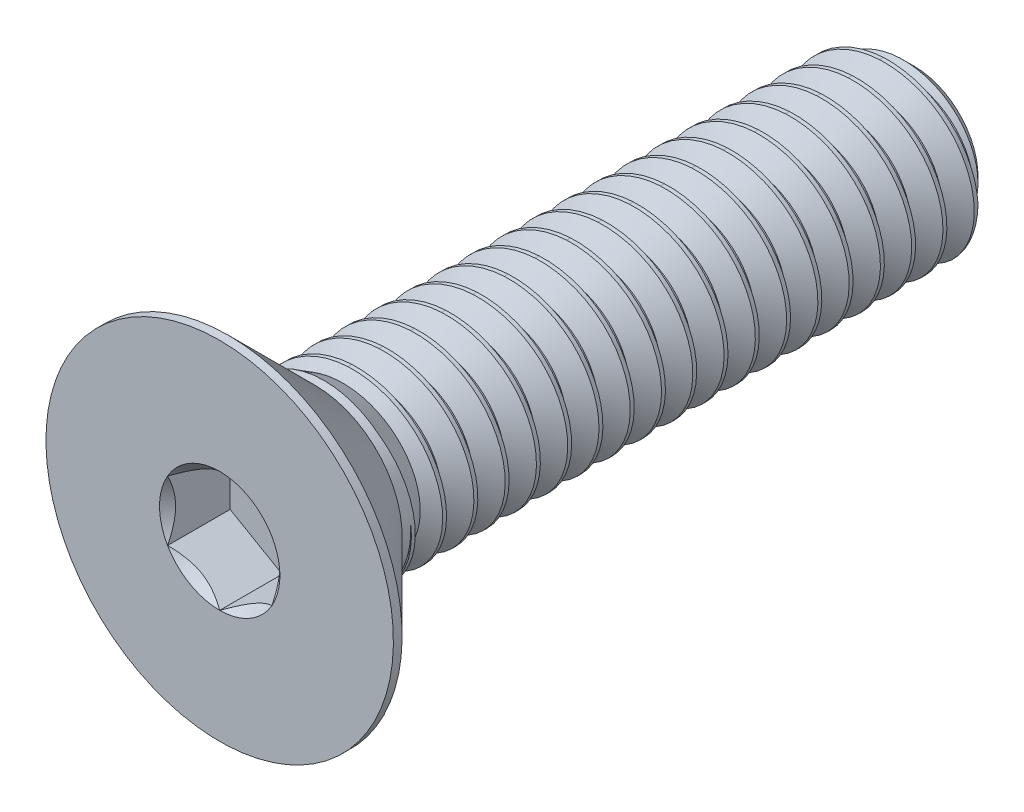
SolidWorks part; units mm, degrees
ref_plane "Front" through (0, 0, 0) normal (0, 0, 1) x (1, 0, 0)
ref_plane "Top" through (0, 0, 0) normal (0, 1, 0) x (1, 0, 0)
ref_plane "Right" through (0, 0, 0) normal (1, 0, 0) x (0, 0, -1)
sketch "Sketch1" plane through (0, 0, 0) normal (0, 0, 1) x (1, 0, 0)
  line L1 (0.75, 0.433) -> (0, 0.866)
  line L8 (0, 0.866) -> (-0.75, 0.433)
  line L9 (-0.75, 0.433) -> (-0.75, -0.433)
  line L10 (-0.75, -0.433) -> (0, -0.866)
  line L11 (0, -0.866) -> (0.75, -0.433)
  line L12 (0.75, -0.433) -> (0.75, 0.433)
  circle A0 centre (0, 0) radius 0.75 construction
  circle A1 centre (0, 0) radius 2.5
  point P7 (0, 2.5)
  dimension "Head Dia" = 5
  dimension "Hex" = 1.5
sketch "Sketch2" plane through (0, 0, 0) normal (1, 0, 0) x (0, 0, -1)
  line L2 (0, 0) -> (8.5, 0) construction
  line L3 (8.5, 0) -> (8.5, 1.25)
  line L6 (8.5, 1.25) -> (0, 1.25)
  line L8 (0, 1.25) -> (-0.125, 1.25)
  line L9 (-0.125, 1.25) -> (-1.375, 2.5)
  line L11 (-1.375, 2.5) -> (-1.5, 2.5)
  line L13 (-1.5, 2.5) -> (-1.5, 0)
  line L14 (-1.5, 0) -> (0, 0) construction
  line L15 (8.4719, 1.2987) -> (8.6969, 0.909) construction
  line L16 (8.6969, 0.909) -> (8.9219, 1.2987) construction
  line L17 (8.9219, 1.2987) -> (8.4719, 1.2987) construction
  line L18 (8.4859, 1.2744) -> (8.9078, 1.2744)
  line L19 (8.9078, 1.2744) -> (8.725, 0.9577)
  line L20 (8.725, 0.9577) -> (8.6688, 0.9577)
  line L21 (8.6688, 0.9577) -> (8.4859, 1.2744)
  line L22 (8.6969, 0.9577) -> (8.6969, 0.909) construction
  line L23 (8.5, 1.25) -> (8.8938, 1.25) construction
  line L24 (8.6969, 1.2987) -> (8.6969, 1.25) construction
  line L25 (8.5, 0.9125) -> (8.1625, 1.25)
  line L26 (8.5, -1.25) -> (0, -1.25)
  point P28 (8.6969, 1.2744)
  point P32 (7.825, -1.25)
  point P33 (-0.6, 0)
  point P35 (-1.5, 2.5)
  dimension "Dia" = 2.5
  dimension "Head Ht" = 1.5
  dimension "D2" = 45
  dimension "Lg" = 10
  dimension "Pitch" = 0.45
  dimension "D3" = 0.0563
  dimension "D1" = 45
  dimension "D4" = 0.3375
  dimension "D5" = 0.675
  dimension "D6" = 0.9
sketch "Sketch7" plane through (0, 0, 0) normal (1, 0, 0) x (0, 0, -1)
  line L2 (-1.5, 0) -> (-1.5, 2.5)
  line L3 (-1.5, 2.5) -> (-1.375, 2.5)
  line L5 (-1.375, 2.5) -> (-0.125, 1.25)
  line L6 (-0.125, 1.25) -> (8.1625, 1.25)
  line L8 (8.1625, 1.25) -> (8.5, 0.9125)
  line L9 (8.5, 0.9125) -> (8.5, 0)
  line L11 (8.5, 0) -> (-1.5, 0)
revolve "Revolve2" add sketch "Sketch7" angle 360 mid plane about L11
sketch "Sketch5" plane through (0, 0, 1.5) normal (0, 0, 1) x (1, 0, 0)
  line L0 (0.75, -0.433) -> (0.75, 0.433) construction
  line L1 (0, -0.866) -> (0.75, -0.433) construction
  line L2 (-0.75, -0.433) -> (0, -0.866) construction
  line L3 (-0.75, 0.433) -> (-0.75, -0.433) construction
  line L4 (0, 0.866) -> (-0.75, 0.433) construction
  line L5 (0.75, 0.433) -> (0, 0.866) construction
  line L6 (0.75, -0.433) -> (0.75, 0.433)
  line L7 (0, -0.866) -> (0.75, -0.433)
  line L8 (-0.75, -0.433) -> (0, -0.866)
  line L9 (-0.75, 0.433) -> (-0.75, -0.433)
  line L10 (0, 0.866) -> (-0.75, 0.433)
  line L11 (0.75, 0.433) -> (0, 0.866)
extrude "Cut-Extrude2" cut sketch "Sketch5" against normal up to vertex (0.9 mm away) up to point (0, 0, 0.6)
sketch "Sketch6" plane through (0, 0, 1.5) normal (0, 0, 1) x (1, 0, 0)
  circle A0 centre (0, 0) radius 0.866
extrude "Cut-Extrude3" cut sketch "Sketch6" against normal up to vertex (0.9 mm away) draft 45 up to point (0, 0, 0.6)
sketch "Sketch3" plane through (0, 0, -8.5) normal (0, 0, -1) x (-1, 0, 0)
  circle A0 centre (0, 0) radius 1.25
split "Split1" trim tools "Front" bodies to split 113 resulting bodies 125 126
curve "Helix/Spiral1" pitch 0.45 height 8.95 turns 19.8889
sketch "Sketch8" plane through (0, 0, 0) normal (1, 0, 0) x (0, 0, -1)
  line L0 (8.4859, 1.2744) -> (8.9078, 1.2744) construction
  line L1 (8.6688, 0.9577) -> (8.4859, 1.2744) construction
  line L2 (8.725, 0.9577) -> (8.6688, 0.9577) construction
  line L3 (8.9078, 1.2744) -> (8.725, 0.9577) construction
  line L4 (8.4859, 1.2744) -> (8.9078, 1.2744)
  line L5 (8.6688, 0.9577) -> (8.4859, 1.2744)
  line L6 (8.725, 0.9577) -> (8.6688, 0.9577)
  line L7 (8.9078, 1.2744) -> (8.725, 0.9577)
sweep "Cut-Sweep1" cut profiles "Sketch8" path "Helix/Spiral1"
sketch "Sketch9" plane through (0, 0, 0) normal (0, 0, 1) x (1, 0, 0)
  circle A0 centre (0, 0) radius 1.25
extrude "Boss-Extrude1" add sketch "Sketch9" against normal up to vertex (8.5 mm away) draft 30.9 up to point (0, 0, -8.5)
equation "\"D3@Helix/Spiral1\" =  ( \"Lg@Sketch2\" - \"Head Ht@Sketch2\" )  + \"Pitch@Sketch2\""
equation "\"D1\"= \"Head Ht@Sketch2\" * .7"
equation "\"D1\"= \"D1\""
equation "\"D4@Helix/Spiral1\" = \"Pitch@Sketch2\""
equation "\"D3@Sketch2\" = \"Pitch@Sketch2\" / 8"
equation "\"D4@Sketch2\" = \"Pitch@Sketch2\" * 0.75"
equation "\"D5@Sketch2\" = \"Pitch@Sketch2\" * 1.5"
equation "\"D6@Sketch2\" = \"Head Ht@Sketch2\" * 0.6"
